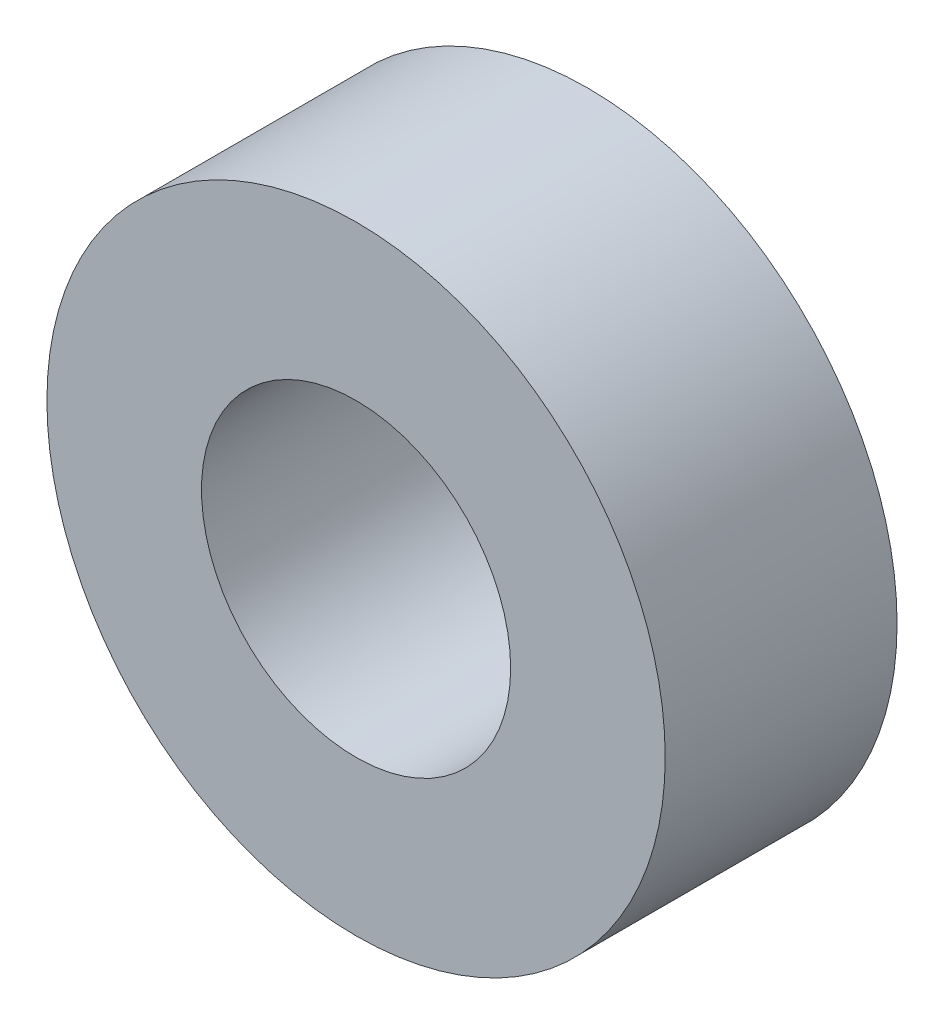
SolidWorks part; units mm, degrees
material "不锈钢 (铁素体)"
ref_plane "前视基准面" through (0, 0, 0) normal (0, 0, 1) x (1, 0, 0)
ref_plane "上视基准面" through (0, 0, 0) normal (0, 1, 0) x (1, 0, 0)
ref_plane "右视基准面" through (0, 0, 0) normal (1, 0, 0) x (0, 0, -1)
sketch "草图1" plane through (0, 0, 0) normal (0, 0, 1) x (1, 0, 0)
  circle A0 centre (0, 0) radius 3
  circle A1 centre (0, 0) radius 6
  dimension "D1" = 6
  dimension "D2" = 12
extrude "凸台-拉伸1" add sketch "草图1" along normal blind 4.5
